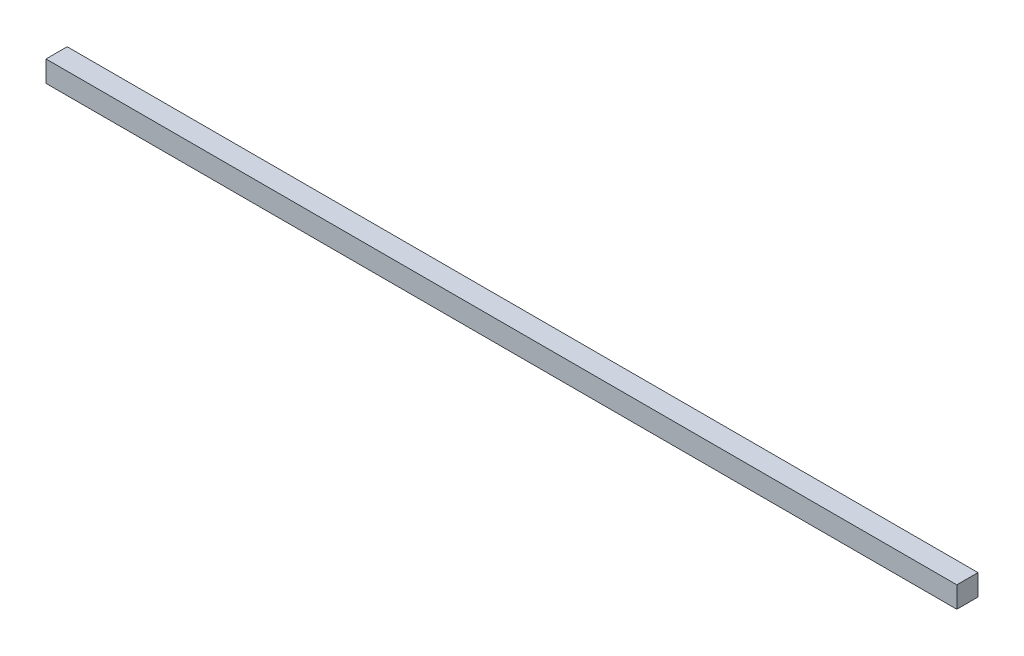
SolidWorks part; units mm, degrees
ref_plane "Front Plane" through (0, 0, 0) normal (0, 0, 1) x (1, 0, 0)
ref_plane "Top Plane" through (0, 0, 0) normal (0, 1, 0) x (1, 0, 0)
ref_plane "Right Plane" through (0, 0, 0) normal (1, 0, 0) x (0, 0, -1)
sketch "Sketch1" plane through (0, 0, 0) normal (0, 1, 0) x (1, 0, 0)
  line L0 (-215, 5) -> (215, -5) construction
  line L1 (-215, 5) -> (215, 5)
  line L2 (-215, 5) -> (-215, -5)
  line L3 (-215, -5) -> (215, -5)
  line L4 (215, 5) -> (215, -5)
  dimension "D1" = 430
  dimension "D2" = 10
extrude "Boss-Extrude1" add sketch "Sketch1" along normal blind 10
